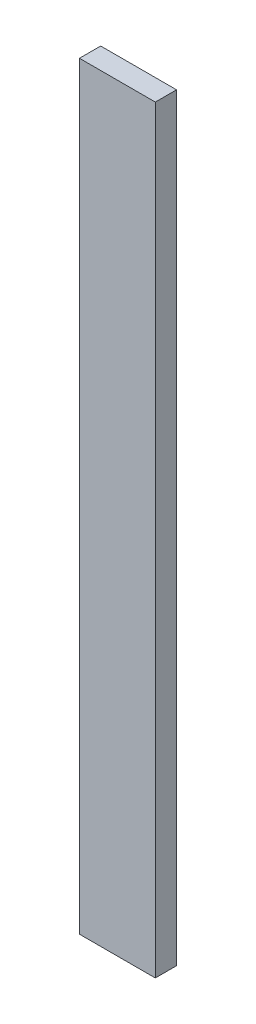
SolidWorks part; units mm, degrees
ref_plane "Спереди" through (0, 0, 0) normal (0, 0, 1) x (1, 0, 0)
ref_plane "Сверху" through (0, 0, 0) normal (0, 1, 0) x (1, 0, 0)
ref_plane "Справа" through (0, 0, 0) normal (1, 0, 0) x (0, 0, -1)
sketch "Эскиз1" plane through (0, 0, 0) normal (0, 1, 0) x (1, 0, 0)
  line L1 (0, 5.5979) -> (20, 5.5979)
  line L2 (0, 5.5979) -> (0, 0)
  line L3 (0, 0) -> (20, 0)
  line L4 (20, 5.5979) -> (20, 0)
  point P4 (0, 0)
extrude "Бобышка-Вытянуть1" add sketch "Эскиз1" along normal blind 200
